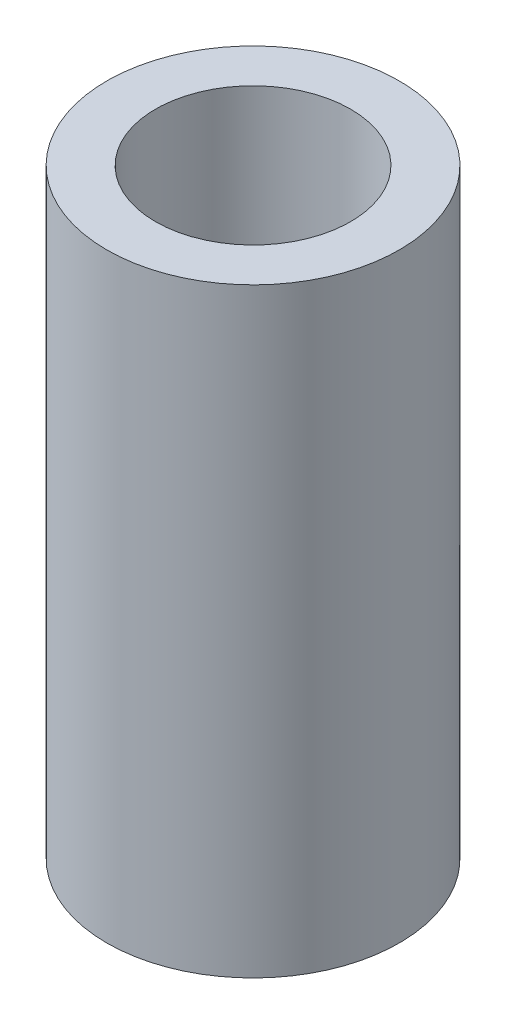
SolidWorks part; units mm, degrees
ref_plane "Front" through (0, 0, 0) normal (0, 0, 1) x (1, 0, 0)
ref_plane "Top" through (0, 0, 0) normal (0, 1, 0) x (1, 0, 0)
ref_plane "Right" through (0, 0, 0) normal (1, 0, 0) x (0, 0, -1)
sketch "Sketch2" plane through (0, 0, 0) normal (0, 1, 0) x (1, 0, 0)
  circle A0 centre (0, 0) radius 1.95
  circle A1 centre (0, 0) radius 1.3
  dimension "D1" = 3.9
  dimension "D2" = 2.6
extrude "Boss-Extrude1" add sketch "Sketch2" along normal blind 8
